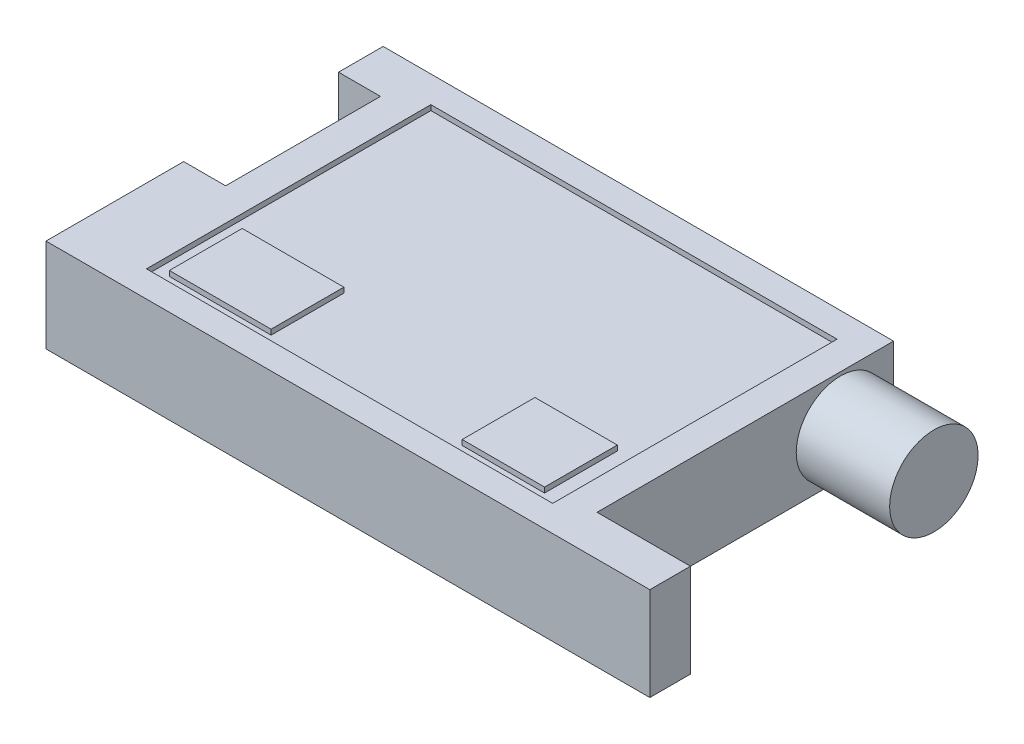
SolidWorks part; units mm, degrees
ref_plane "Front Plane" through (0, 0, 0) normal (0, 0, 1) x (1, 0, 0)
ref_plane "Top Plane" through (0, 0, 0) normal (0, 1, 0) x (1, 0, 0)
ref_plane "Right Plane" through (0, 0, 0) normal (1, 0, 0) x (0, 0, -1)
sketch "Sketch1" plane through (0, 0, 0) normal (0, 1, 0) x (1, 0, 0)
  line L0 (-55.6025, 28.3587) -> (-55.6025, 19.7686)
  line L1 (-55.6025, 19.7686) -> (-47.5188, 19.7686)
  line L2 (-47.5188, 19.7686) -> (-47.5188, -10.0553)
  line L3 (-47.5188, -10.0553) -> (-55.6025, -10.0553)
  line L4 (-55.6025, -10.0553) -> (-55.6025, -36.5714)
  line L5 (-55.6025, -36.5714) -> (60.6979, -36.5714)
  line L6 (60.6979, -36.5714) -> (60.6979, -28.7485)
  line L7 (60.6979, -28.7485) -> (42.7053, -28.7485)
  line L8 (42.7053, -28.7485) -> (42.7053, 13.756)
  line L9 (42.7053, 13.756) -> (42.7053, 28.3587)
  line L10 (42.7053, 28.3587) -> (-55.6025, 28.3587)
extrude "Boss-Extrude1" add sketch "Sketch1" along normal blind 18
sketch "Sketch2" plane through (42.7053, 0, 0) normal (1, 0, 0) x (0, 0, -1)
  circle A0 centre (18.1337, 8.781) radius 8.5167
extrude "Boss-Extrude2" add sketch "Sketch2" along normal up to surface (17.9927 mm away) up to face at (60.6979, 9, 32.6599)
sketch "Sketch3" plane through (0, 18, 0) normal (0, 1, 0) x (1, 0, 0)
  line L0 (-41.2893, 23.244) -> (-41.2893, -31.5331)
  line L1 (-41.2893, -31.5331) -> (36.945, -31.5331)
  line L2 (36.945, -31.5331) -> (36.945, 23.244)
  line L3 (36.945, 23.244) -> (-41.2893, 23.244)
extrude "Cut-Extrude1" cut sketch "Sketch3" against normal blind 1
sketch "Sketch4" plane through (0, 17, 0) normal (0, 1, 0) x (1, 0, 0)
  line L1 (17.5789, -15.5786) -> (33.4416, -15.5786)
  line L2 (17.5789, -15.5786) -> (17.5789, -29.5927)
  line L3 (17.5789, -29.5927) -> (33.4416, -29.5927)
  line L4 (33.4416, -15.5786) -> (33.4416, -29.5927)
  line L5 (-38.8119, -15.5786) -> (-19.2267, -15.5786)
  line L6 (-38.8119, -15.5786) -> (-38.8119, -29.5927)
  line L7 (-38.8119, -29.5927) -> (-19.2267, -29.5927)
  line L8 (-19.2267, -15.5786) -> (-19.2267, -29.5927)
extrude "Boss-Extrude3" add sketch "Sketch4" along normal up to surface (1 mm away) up to face at (-2.1721, 18, 4.1445)
sketch "Sketch5" plane through (0, 0, -19.7686) normal (0, 0, 1) x (1, 0, 0)
  line L0 (-47.5188, 18) -> (-47.5188, 0) construction
  line L1 (-47.5188, 4.0209) -> (-51.6294, 4.0209)
  line L2 (-47.5188, 4.0209) -> (-47.5188, 13.4254)
  line L3 (-47.5188, 13.4254) -> (-51.6294, 13.4254)
  line L4 (-51.6294, 4.0209) -> (-51.6294, 13.4254)
extrude "Cut-Extrude2" cut sketch "Sketch5" against normal through all
